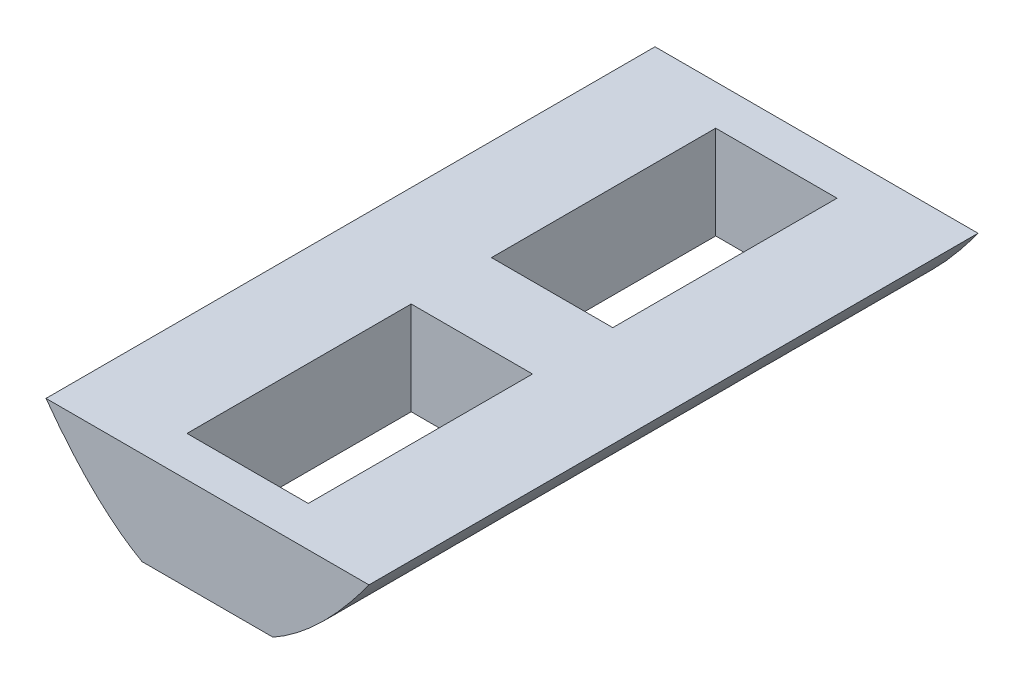
SolidWorks part; units mm, degrees
ref_plane "Front Plane" through (0, 0, 0) normal (0, 0, 1) x (1, 0, 0)
ref_plane "Top Plane" through (0, 0, 0) normal (0, 1, 0) x (1, 0, 0)
ref_plane "Right Plane" through (0, 0, 0) normal (1, 0, 0) x (0, 0, -1)
sketch "Sketch2" plane through (0, 0, 0) normal (0, 0, 1) x (1, 0, 0)
  line L0 (-127, 127) -> (127, 127)
  spline S0 degree 2 poles (-143.0272, 161.0769) (0, -161.0769) (143.0272, 161.0769) knots 0 0 0 1 1 1 construction
  spline S1 degree 2 poles (-127, 127) (0, -127) (127, 127) knots 0.056028 0.056028 0.056028 0.943972 0.943972 0.943972
extrude "Boss-Extrude2" add sketch "Sketch2" along normal blind 331.382
sketch "Sketch3" plane through (0, 127, 0) normal (0, 1, 0) x (1, 0, 0)
  line L0 (0, -309.5365) -> (0, 0) construction
  line L1 (-33, -21.8455) -> (33, -21.8455)
  line L2 (-33, -21.8455) -> (-33, -143.8455)
  line L3 (-33, -143.8455) -> (33, -143.8455)
  line L4 (33, -21.8455) -> (33, -143.8455)
  line L5 (-33, -187.5365) -> (33, -187.5365)
  line L6 (-33, -187.5365) -> (-33, -309.5365)
  line L7 (-33, -309.5365) -> (33, -309.5365)
  line L8 (33, -187.5365) -> (33, -309.5365)
  line L9 (-127, -165.691) -> (127, -165.691) construction
  line L10 (-127, -331.382) -> (-127, 0) construction
  line L11 (127, -331.382) -> (127, 0) construction
  line L12 (-33, -143.8455) -> (-33, -165.691) construction
  line L13 (33, -187.5365) -> (33, -165.691) construction
  line L14 (-33, -21.8455) -> (-33, 0) construction
  line L15 (127, 0) -> (-127, 0) construction
  dimension "D1" = 122
  dimension "D2" = 66
extrude "Cut-Extrude2" cut sketch "Sketch3" against normal through all
sketch "Sketch4" plane through (0, 0, 0) normal (0, 0, -1) x (-1, 0, 0)
  line L1 (-40, 10) -> (40, 10)
  line L2 (-40, 10) -> (-40, 0)
  line L3 (-40, 0) -> (40, 0)
  line L4 (40, 10) -> (40, 0)
  dimension "D1" = 10
  dimension "D2" = 80
extrude "Cut-Extrude3" cut sketch "Sketch4" against normal through all
sketch "Sketch5" plane through (0, 0, 331.382) normal (0, 0, 1) x (1, 0, 0)
  line L0 (0, 0) -> (0, 60.8) construction
  line L1 (-130, 130.8) -> (130, 130.8)
  line L2 (-130, 130.8) -> (-130, 60.8)
  line L3 (-130, 60.8) -> (130, 60.8)
  line L4 (130, 130.8) -> (130, 60.8)
  dimension "D1" = 60.8
  dimension "D2" = 260
  dimension "D3" = 70
extrude "Cut-Extrude4" cut sketch "Sketch5" against normal through all
